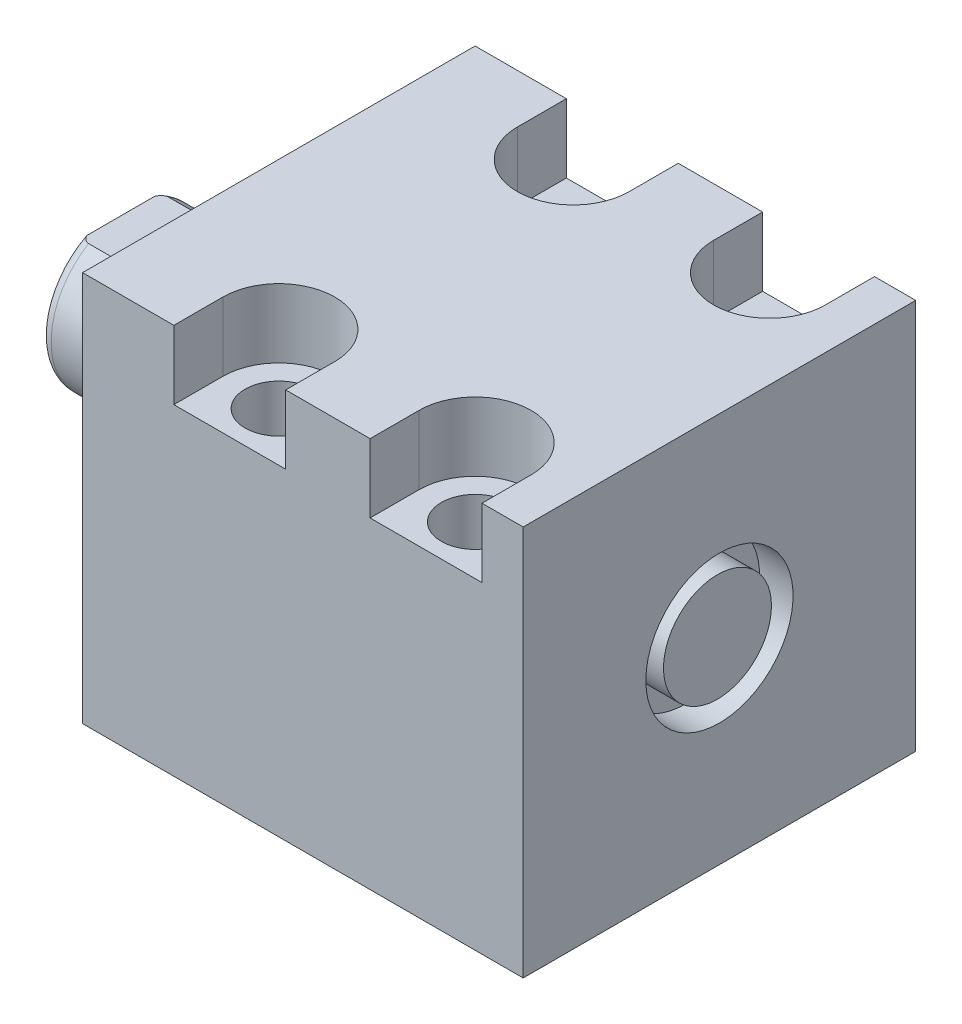
SolidWorks part; units mm, degrees
material "Alloy Steel"
ref_plane "Front Plane" through (0, 0, 0) normal (0, 0, 1) x (1, 0, 0)
ref_plane "Top Plane" through (0, 0, 0) normal (0, 1, 0) x (1, 0, 0)
ref_plane "Right Plane" through (0, 0, 0) normal (1, 0, 0) x (0, 0, -1)
ref_plane "Plane1" through (0, 0, 0) normal (1, 0, 0) x (0, 0, -1)
sketch "Sketch1" plane through (0, 0, 0) normal (1, 0, 0) x (0, 0, -1)
  line L0 (-25.4, 25.146) -> (25.4, 25.146)
  line L1 (25.4, 25.146) -> (25.4, -25.4)
  line L2 (25.4, -25.4) -> (-25.4, -25.4)
  line L3 (-25.4, -25.4) -> (-25.4, 25.146)
  line L4 (0, -24.4475) -> (0, 24.4475) construction
  dimension "D1" = 50.546
  dimension "D2" = 25.4
  dimension "D3" = 50.8
  dimension "D4" = 25.4
extrude "Extrude1" add sketch "Sketch1" along normal blind 57.02
sketch "Sketch5" plane through (0, 0, 0) normal (-1, 0, 0) x (0, 0, 1)
  circle A0 centre (0, 0) radius 17.4625
  dimension "D1" = 34.925
extrude "Extrude2" add sketch "Sketch5" along normal blind 5.969
ref_plane "Plane5" through (0, 0, 0) normal (0, -1, 0) x (0, 0, 1)
sketch "Sketch6" plane through (0, 0, 0) normal (0, -1, 0) x (0, 0, 1)
  line L0 (0, 5.969) -> (-10.3187, 5.969)
  line L1 (-10.3187, 5.969) -> (-10.3187, 20.45)
  line L2 (-10.3187, 20.45) -> (0, 20.45)
  line L3 (0, 20.45) -> (0, 5.969)
  line L4 (0, -5.7546) -> (0, 21.1709) construction
  line L5 (17.4625, 5.969) -> (-17.4625, 5.969) construction
  line L6 (25.4, -57.02) -> (-25.4, -57.02) construction
  dimension "D1" = 77.47
  dimension "D2" = 20.6375
revolve "Revolve1" add sketch "Sketch6" angle 360 about L4
ref_plane "Plane6" through (-18.5113, 3.2639, 0) normal (0, 0, 1) x (0, 1, 0)
sketch "S2D0001" plane through (-18.5113, 3.2639, 0) normal (0, 0, 1) x (0, 1, 0)
  line L0 (0, 0.003) -> (0, -14.6475)
  line L2 (1.1176, 1.9387) -> (-3.2639, 1.9387)
  line L3 (-3.2639, 1.9387) -> (-3.2639, -14.6475)
  line L4 (0, 0.003) -> (1.1176, 1.9387)
  line L5 (-3.2639, -18.5113) -> (-3.2639, 2.765) construction
  line L6 (7.0549, 1.9387) -> (-13.5826, 1.9387) construction
  line L7 (0, -14.6475) -> (-3.2639, -14.6475)
  dimension "D1" = 30
  dimension "D2" = 8.763
  dimension "D3" = 6.5278
  dimension "D4" = 16.5862
revolve "Cut-Revolve4" cut sketch "S2D0001" angle 360 about L5
ref_plane "Plane7" through (0, 0, 0) normal (0, 1, 0) x (0, 0, -1)
sketch "Sketch8" plane through (0, 0, 0) normal (0, 1, 0) x (0, 0, -1)
  line L0 (-10.3187, 13.0332) -> (-10.033, 13.7952)
  line L1 (-10.033, 13.7952) -> (-10.033, 19.434)
  line L2 (0, 12.6594) -> (0, 20.8178) construction
  line L3 (-10.3187, 13.0332) -> (-10.3187, 20.45)
  line L4 (-9.6449, 20.45) -> (-10.3187, 20.45)
  line L5 (10.3187, 20.45) -> (-10.3187, 20.45) construction
  line L6 (-10.3187, 20.45) -> (-10.3187, 5.969) construction
  arc A0 (-9.6449, 20.45) -> (-10.033, 19.434) centre (-8.509, 19.434) ccw
  dimension "D2" = 1.524
  dimension "D1" = 20.066
  dimension "D3" = 1.016
  dimension "D4" = 0.762
  dimension "D5" = 6.6548
revolve "Cut-Revolve5" cut sketch "Sketch8" angle 360 about L2
ref_plane "Plane11" through (0, 0, 0) normal (0, 0, -1) x (0, -1, 0)
sketch "Sketch12" plane through (0, 0, 0) normal (0, 0, -1) x (0, -1, 0)
  line L0 (8.5852, 20.45) -> (8.5852, 15.497)
  line L1 (8.5852, 15.497) -> (10.033, 14.0492)
  line L2 (-8.5852, 20.45) -> (-8.5852, 15.497)
  line L3 (-8.5852, 15.497) -> (-10.033, 14.0492)
  line L4 (8.5852, 20.45) -> (10.033, 20.45)
  line L5 (0, 13.7262) -> (0, 20.767) construction
  line L6 (-10.033, 14.0492) -> (-10.033, 20.45)
  line L8 (10.033, 13.7952) -> (10.033, 19.434) construction
  line L9 (10.033, 14.0492) -> (10.033, 20.45)
  line L10 (-8.5852, 20.45) -> (-10.033, 20.45)
  line L12 (9.6449, 20.45) -> (-9.6449, 20.45) construction
  dimension "D1" = 17.1704
  dimension "D2" = 4.953
  dimension "D3" = 45
extrude "Cut-Extrude4" cut sketch "Sketch12" against normal mid plane 60.96
hole_wizard "Hole2" positions "Sketch17" profile "Sketch16" legacy
sketch "Sketch17" plane through (0, 25.146, 0) normal (0, 1, 0) x (-1, 0, 0)
  line L0 (0, 0) -> (-59.3363, 0) construction
  line L1 (0, -25.4) -> (0, 25.4) construction
  point P0 (-19.05, -19.05)
  point P9 (-19.05, 19.05)
  dimension "D1" = 38.1
  dimension "D2" = 19.05
sketch "Sketch16" plane through (19.05, 25.146, -19.05) normal (1, 0, 0) x (0, 0, 1)
  line L0 (0, 0) -> (0, 50.546)
  line L1 (0, 50.546) -> (4.3688, 50.546)
  line L2 (4.3688, 50.546) -> (4.3688, 0)
  line L3 (4.3688, 0) -> (0, 0)
  line L4 (0, 110) -> (0, -10) construction
  dimension "Diameter" = 8.7376
  dimension "Depth" = 50.546
pattern_linear "LPattern1" count 2 spacing 25.4 along (1, 0, 0) of "Hole2"
sketch "Sketch18" plane through (0, 25.146, 0) normal (0, 1, 0) x (1, 0, 0)
  line L0 (0, 0) -> (50.053, 0) construction
  line L2 (57.02, -25.4) -> (0, -25.4) construction
  line L4 (51.689, -25.4) -> (37.211, -25.4)
  line L5 (11.811, -19.05) -> (11.811, -25.4)
  line L6 (26.289, -19.05) -> (26.289, -25.4)
  line L7 (37.211, -19.05) -> (37.211, -25.4)
  line L8 (51.689, 19.05) -> (51.689, 25.4)
  line L9 (26.289, -25.4) -> (11.811, -25.4)
  line L12 (26.289, 25.4) -> (11.811, 25.4)
  line L14 (37.211, 19.05) -> (37.211, 25.4)
  line L15 (26.289, 19.05) -> (26.289, 25.4)
  line L16 (11.811, 19.05) -> (11.811, 25.4)
  line L17 (51.689, 25.4) -> (37.211, 25.4)
  line L18 (51.689, -19.05) -> (51.689, -25.4)
  arc A0 (26.289, -19.05) -> (11.811, -19.05) centre (19.05, -19.05) ccw
  arc A1 (51.689, -19.05) -> (37.211, -19.05) centre (44.45, -19.05) ccw
  arc A2 (51.689, 19.05) -> (37.211, 19.05) centre (44.45, 19.05) cw
  arc A3 (26.289, 19.05) -> (11.811, 19.05) centre (19.05, 19.05) cw
  dimension "D1" = 14.478
extrude "Cut-Extrude5" cut sketch "Sketch18" against normal blind 8.89
hole_wizard "Hole3" positions "Sketch20" profile "Sketch19" legacy
sketch "Sketch20" plane through (0, -25.4, 0) normal (0, -1, 0) x (1, 0, 0)
  line L0 (0, 25.4) -> (0, -25.4) construction
  point P0 (12.7, 0)
  dimension "D1" = 12.7
sketch "Sketch19" plane through (12.7, -25.4, 0) normal (1, 0, 0) x (0, 0, -1)
  line L0 (0, 0) -> (0, 12.2569)
  line L1 (0, 12.2569) -> (1.5875, 11.303)
  line L2 (1.5875, 11.303) -> (1.5875, 1.4478)
  line L3 (1.5875, 1.4478) -> (5.6705, 1.4478)
  line L4 (5.6705, 0) -> (0, 0)
  line L5 (0, -11.3109) -> (0, 121.1557) construction
  line L6 (0, 12.2569) -> (-1.5875, 11.303) construction
  line L7 (5.6705, 1.4478) -> (5.6705, 0)
  dimension "Depth" = 11.303
  dimension "Drill Angle" = 118
  dimension "Diameter" = 3.175
  dimension "C-Bore Diameter" = 11.3411
  dimension "C-Bore Depth" = 1.4478
hole_wizard "Hole4" positions "Sketch21" profile "Sketch22" legacy
sketch "Sketch21" plane through (0, -25.4, 0) normal (0, -1, 0) x (1, 0, 0)
  point P0 (38.1, 0)
  dimension "D1" = 25.4
sketch "Sketch22" plane through (38.1, -25.4, 0) normal (1, 0, 0) x (0, 0, -1)
  line L0 (0, 0) -> (0, 14.8223)
  line L1 (0, 14.8223) -> (1.5875, 13.8684)
  line L2 (1.5875, 13.8684) -> (1.5875, 1.4478)
  line L3 (1.5875, 1.4478) -> (5.6705, 1.4478)
  line L4 (5.6705, 0) -> (0, 0)
  line L5 (0, -11.3109) -> (0, 121.1557) construction
  line L6 (0, 14.8223) -> (-1.5875, 13.8684) construction
  line L7 (5.6705, 1.4478) -> (5.6705, 0)
  dimension "Depth" = 13.8684
  dimension "Drill Angle" = 118
  dimension "Diameter" = 3.175
  dimension "C-Bore Diameter" = 11.3411
  dimension "C-Bore Depth" = 1.4478
chamfer "Chamfer1" distance 0.635 angle 45 2 edges at (38.1, -23.9522, -1.5875) (12.7, -23.9522, -1.5875)
sketch "Sketch23" plane through (0, 0, 0) normal (0, 0, 1) x (1, 0, 0)
  line L0 (12.7, -23.9522) -> (12.7, -21.4272) construction
  line L1 (10.4775, -23.9522) -> (14.9225, -23.9522) construction
  line L2 (7.0294, -23.9522) -> (18.3705, -23.9522) construction
  line L3 (7.0294, -23.9522) -> (7.0294, -25.4) construction
  circle A0 centre (8.4772, -25.4) radius 1.4478
  dimension "D1" = 2.8956
revolve "Revolve2" add sketch "Sketch23" angle 360 about L0
pattern_linear "LPattern3" count 2 spacing 25.4 along (1, 0, 0) of bodies 128
sketch "Sketch24" plane through (0, 0, 0) normal (0, 0, 1) x (1, 0, 0)
  line L0 (0, 0) -> (74.772, 0) construction
  line L1 (57.02, 9.525) -> (52.702, 9.525)
  line L2 (57.02, 25.146) -> (57.02, -25.4) construction
  line L3 (52.702, 9.525) -> (52.702, 0)
  line L8 (52.702, 0) -> (57.02, 0)
  line L9 (57.02, 0) -> (57.02, 9.525)
  dimension "D1" = 4.318
  dimension "D2" = 19.05
revolve "Cut-Revolve6" cut sketch "Sketch24" angle 360 about L0
sketch "Sketch25" plane through (52.702, 0, 0) normal (1, 0, 0) x (0, 0, -1)
  circle A0 centre (0, 0) radius 6.985
  circle A1 centre (0, 0) radius 9.525 construction
  dimension "D1" = 13.97
extrude "Extrude3" add sketch "Sketch25" along normal blind 4.064
